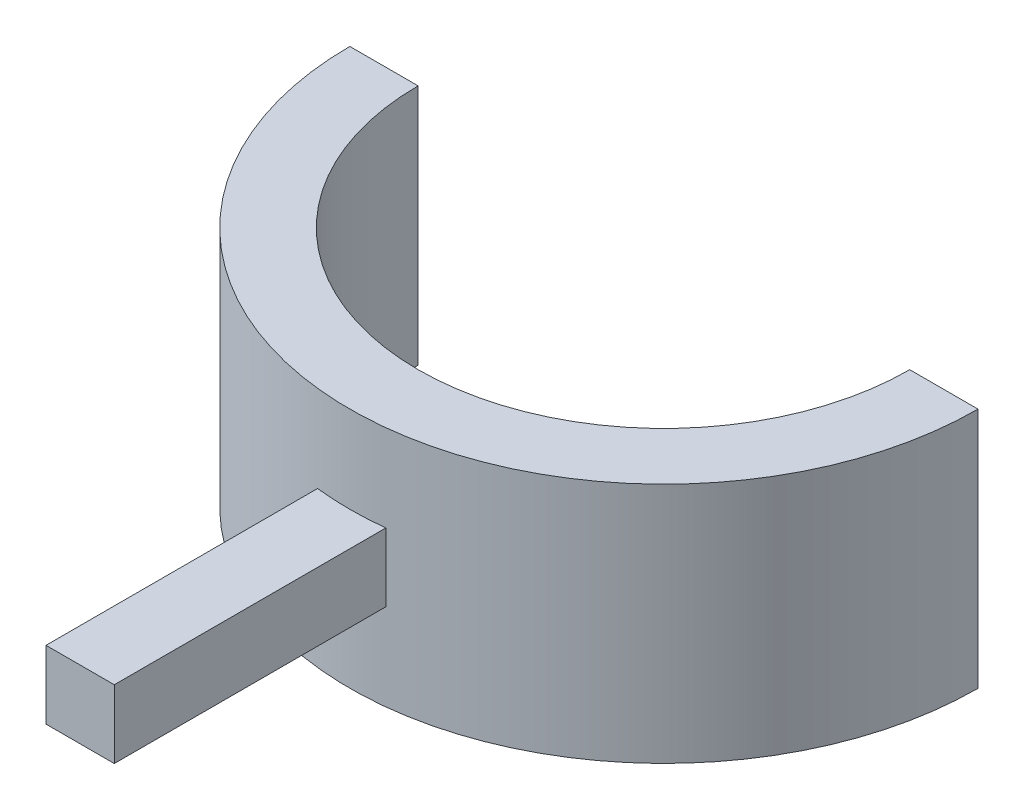
SolidWorks part; units mm, degrees
ref_plane "Front Plane" through (0, 0, 0) normal (0, 0, 1) x (1, 0, 0)
ref_plane "Top Plane" through (0, 0, 0) normal (0, 1, 0) x (1, 0, 0)
ref_plane "Right Plane" through (0, 0, 0) normal (1, 0, 0) x (0, 0, -1)
sketch "Sketch1" plane through (0, 0, 0) normal (0, 1, 0) x (1, 0, 0)
  line L0 (23, 23) -> (18, 23)
  line L1 (-18, 23) -> (-23, 23)
  arc A0 (-18, 23) -> (18, 23) centre (0, 23) ccw
  arc A1 (-23, 23) -> (23, 23) centre (0, 23) ccw
extrude "Boss-Extrude1" add sketch "Sketch1" along normal blind 17.71
ref_plane "Plane1" through (0, 0, 0) normal (0, 0, 1) x (1, 0, 0)
sketch "Sketch2" plane through (0, 0, 0) normal (0, 0, 1) x (1, 0, 0)
  line L0 (0, 0) -> (0, 17.71) construction
  line L2 (23, 17.71) -> (-23, 17.71) construction
  line L4 (-2.5, 6.355) -> (2.5, 6.355)
  line L5 (-2.5, 6.355) -> (-2.5, 11.355)
  line L6 (-2.5, 11.355) -> (2.5, 11.355)
  line L7 (2.5, 6.355) -> (2.5, 11.355)
  line L8 (-2.5, 6.355) -> (2.5, 11.355) construction
  line L9 (-2.5, 11.355) -> (2.5, 6.355) construction
  point P5 (0, 8.855)
  dimension "D1" = 5
  dimension "D2" = 5
extrude "Boss-Extrude2" add sketch "Sketch2" along normal blind 19.75 and the other way up to surface separate body
